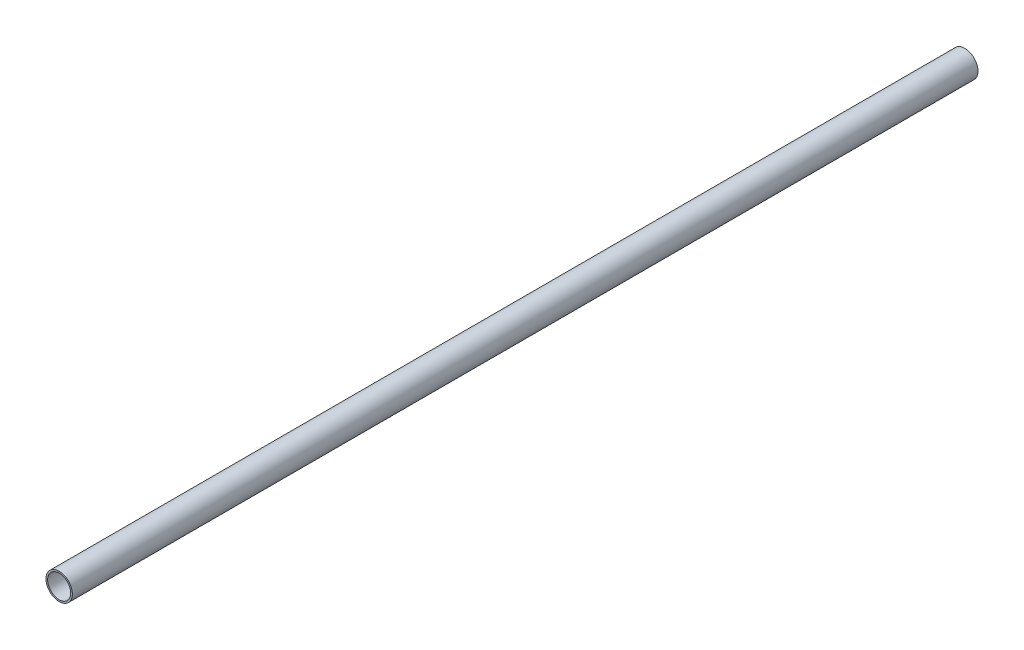
SolidWorks part; units mm, degrees
material "Carbon Fiber Tube - UD Approx"
ref_plane "Front Plane" through (0, 0, 0) normal (0, 0, 1) x (1, 0, 0)
ref_plane "Top Plane" through (0, 0, 0) normal (0, 1, 0) x (1, 0, 0)
ref_plane "Right Plane" through (0, 0, 0) normal (1, 0, 0) x (0, 0, -1)
sketch "Sketch1" plane through (0, 0, 0) normal (0, 0, 1) x (1, 0, 0)
  circle A0 centre (0, 0) radius 8
  circle A1 centre (0, 0) radius 7
  dimension "D1" = 16
  dimension "D2" = 14
extrude "Boss-Extrude1" add sketch "Sketch1" along normal blind 550
